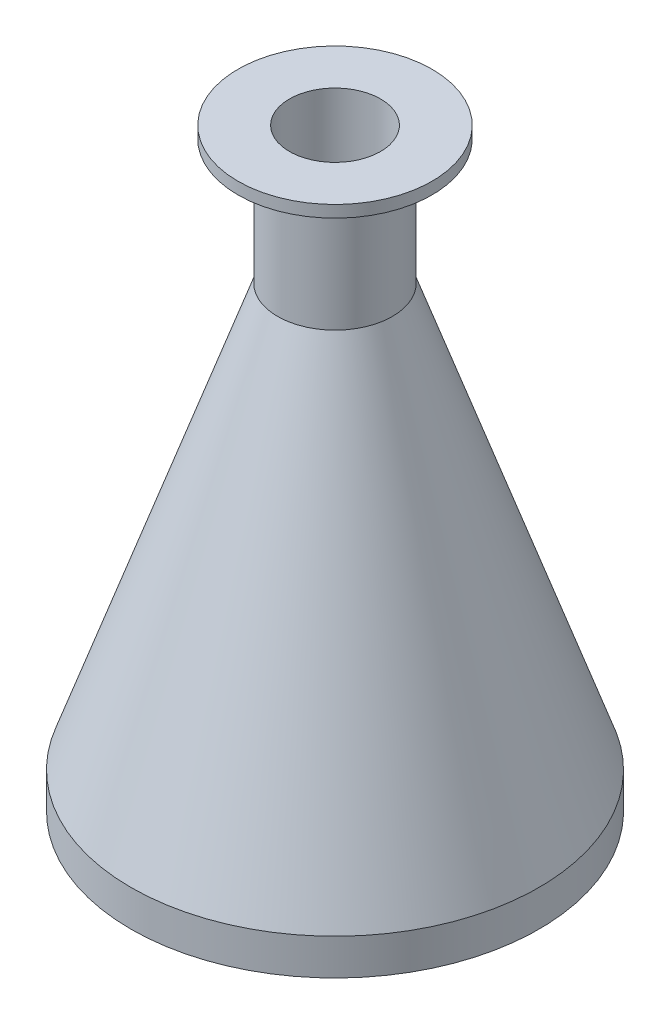
SolidWorks part; units mm, degrees
ref_plane "Front" through (0, 0, 0) normal (0, 0, 1) x (1, 0, 0)
ref_plane "Top" through (0, 0, 0) normal (0, 1, 0) x (1, 0, 0)
ref_plane "Right" through (0, 0, 0) normal (1, 0, 0) x (0, 0, -1)
sketch "Sketch1" plane through (0, 0, 0) normal (0, 0, 1) x (1, 0, 0)
  line L0 (0, 0) -> (0, 150) construction
  line L1 (11.5, 150) -> (11.5, 114.9425)
  line L2 (11.5, 114.9425) -> (51.5, 0)
  line L3 (14.5, 115.4496) -> (14.5, 147)
  line L8 (14.5, 115.4496) -> (51.5, 9.1278)
  line L9 (11.5, 150) -> (14.5, 150)
  line L10 (51.5, 0) -> (51.5, 9.1278)
  line L12 (14.5, 115.4496) -> (54.3333, 0.986) construction
  line L15 (0, 0) -> (51.5, 0) construction
  line L16 (14.5, 150) -> (24.5, 150)
  line L17 (24.5, 150) -> (24.5, 147)
  line L18 (24.5, 147) -> (14.5, 147)
  line L19 (14.5, 144) -> (14.5, 115.4496) construction
  line L20 (14.5, 144) -> (14.5, 144) construction
  line L21 (14.5, 144) -> (14.5, 144) construction
  line L22 (14.5, 144) -> (14.5, 144) construction
  line L23 (14.5, 144) -> (14.5, 144) construction
  dimension "D3" = 150
  dimension "D1" = 3
  dimension "D2" = 51.5
revolve "Revolve1" add sketch "Sketch1" angle 360 about L0
